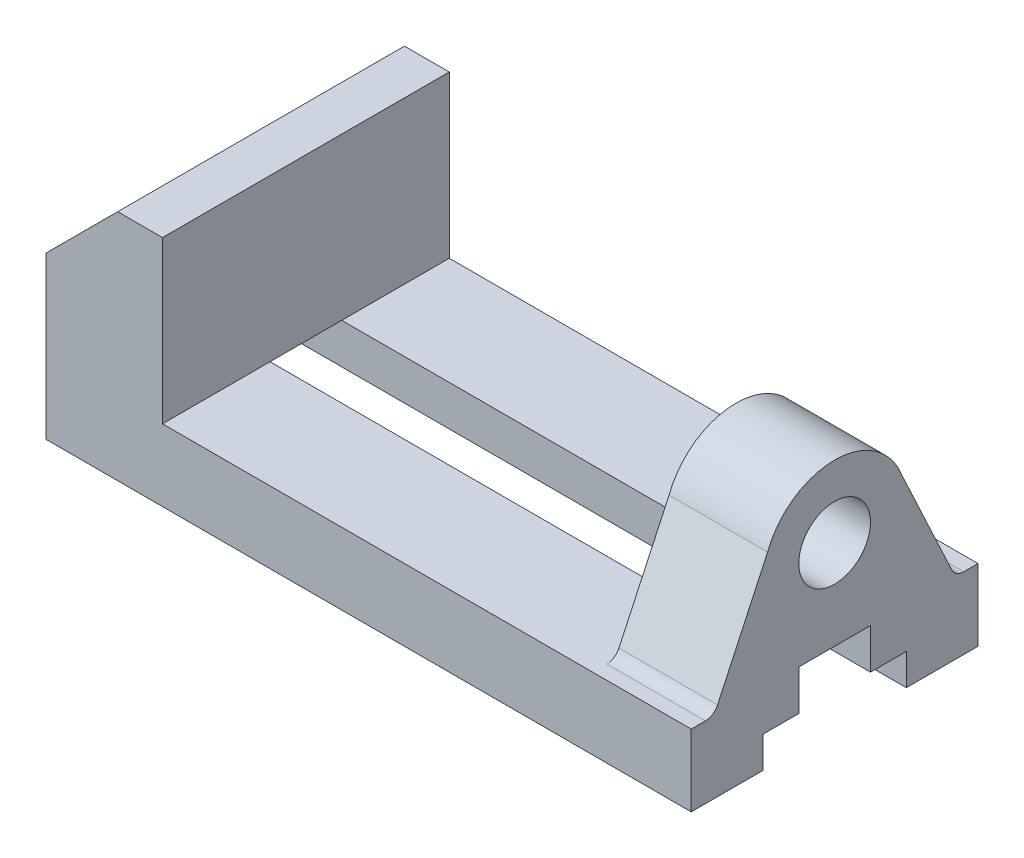
SolidWorks part; units mm, degrees
ref_plane "Front Plane" through (0, 0, 0) normal (0, 0, 1) x (1, 0, 0)
ref_plane "Top Plane" through (0, 0, 0) normal (0, 1, 0) x (1, 0, 0)
ref_plane "Right Plane" through (0, 0, 0) normal (1, 0, 0) x (0, 0, -1)
sketch "Sketch1" plane through (0, 0, 0) normal (0, 1, 0) x (1, 0, 0)
  line L1 (-72, 32) -> (72, 32)
  line L2 (-72, 32) -> (-72, -32)
  line L3 (-72, -32) -> (72, -32)
  line L4 (72, 32) -> (72, -32)
  line L5 (-72, 32) -> (72, -32) construction
  line L6 (-72, -32) -> (72, 32) construction
  point P0 (0, 0)
  dimension "D1" = 64
  dimension "D2" = 144
extrude "Boss-Extrude1" add sketch "Sketch1" along normal blind 16
sketch "Sketch2" plane through (0, 16, 0) normal (0, 1, 0) x (1, 0, 0)
  line L1 (-72, 32) -> (-46, 32)
  line L2 (-72, 32) -> (-72, -32)
  line L3 (-72, -32) -> (-46, -32)
  line L4 (-46, 32) -> (-46, -32)
  dimension "D1" = 26
extrude "Boss-Extrude2" add sketch "Sketch2" along normal blind 36
sketch "Sketch3" plane through (0, 0, 32) normal (0, 0, 1) x (1, 0, 0)
  line L0 (-46, 52) -> (-56, 52)
  line L1 (-72, 52) -> (-46, 52) construction
  line L2 (-56, 52) -> (-72, 36)
  line L3 (-72, 52) -> (-72, 0) construction
  dimension "D1" = 10
  dimension "D3" = 16
extrude "Cut-Extrude1" cut sketch "Sketch3" against normal through all and the other way through all
sketch "Sketch4" plane through (0, 16, 0) normal (0, 1, 0) x (1, 0, 0)
  line L0 (-46, -32) -> (72, -32) construction
  line L1 (72, 32) -> (50, 32)
  line L2 (72, 32) -> (72, -32)
  line L3 (72, -32) -> (50, -32)
  line L4 (50, 32) -> (50, -32)
  dimension "D1" = 22
extrude "Boss-Extrude3" add sketch "Sketch4" along normal blind 36
sketch "Sketch5" plane through (72, 0, 0) normal (1, 0, 0) x (0, 0, -1)
  line L0 (-32, 16) -> (32, 16) construction
  line L1 (-32, 52) -> (-32, 0) construction
  line L2 (32, 52) -> (32, 0) construction
  line L3 (-32, 0) -> (32, 0) construction
  line L4 (-16, 0) -> (-16, 7)
  line L5 (-16, 7) -> (-8, 7)
  line L6 (-8, 7) -> (-8, 16)
  line L7 (-8, 16) -> (8, 16)
  line L8 (8, 16) -> (8, 7)
  line L9 (8, 7) -> (16, 7)
  line L10 (16, 7) -> (16, 0)
  point P10 (0, 0)
  point P17 (0, 0)
  point P19 (0, 16)
  line M1 (-32, 0) -> (32, 0)
  dimension "D1" = 16
  dimension "D2" = 32
  dimension "D3" = 7
  dimension "D4" = 7
  dimension "D5" = 16
  dimension "D6" = 8
extrude "Cut-Extrude2" cut sketch "Sketch5" against normal through all and the other way through all contours L10 L9 L8 L7 L6 L5 L4 M1
sketch "Sketch6" plane through (72, 0, 0) normal (1, 0, 0) x (0, 0, -1)
  line L0 (-32, 16) -> (32, 16) construction
  line L1 (-32, 52) -> (32, 52) construction
  line L2 (-32, 16) -> (-28.8437, 16)
  line L3 (-26.1248, 17.7321) -> (-14.9584, 41.6784)
  line L4 (0, 52) -> (0, 17.0603) construction
  line L5 (26.1248, 17.7321) -> (14.9584, 41.6784)
  line L6 (28.8437, 16) -> (32, 16)
  arc A0 (14.9584, 41.6784) -> (-14.9584, 41.6784) centre (0, 36) ccw
  circle A1 centre (0, 36) radius 8
  arc A2 (26.1248, 17.7321) -> (28.8437, 16) centre (28.8437, 19) ccw
  arc A3 (-28.8437, 16) -> (-26.1248, 17.7321) centre (-28.8437, 19) ccw
  point P17 (26.9325, 16)
  point P20 (-26.9325, 16)
  line M3 (32, 0) -> (32, 52)
  line M4 (32, 52) -> (-32, 52)
  line M5 (-32, 52) -> (-32, 0)
  dimension "D1" = 32
  dimension "D3" = 16
  dimension "D4" = 3
  dimension "D2" = 50
extrude "Cut-Extrude3" cut sketch "Sketch6" against normal blind 36 contours L2 A3 L3 A0 M4 M5 | A1 | L5 A2 L6 A0 M3 M4
hole_wizard "Ø12.0mm Dowel Hole1" positions "Sketch7" profile "Sketch8" hole size "Ø12.0" standard "AS"
sketch "Sketch7" plane through (0, 0, 0) normal (0, -1, 0) x (-1, 0, 0)
  line L0 (72, -16) -> (72, -32) construction
  line L1 (72, 32) -> (72, 16) construction
  point P0 (34, -23.5518)
  point P2 (-36, -23.5518)
  point P4 (-36, 24.9579)
  point P6 (34, 24.9579)
  dimension "D1" = 38
  dimension "D2" = 70
  dimension "D3" = 38
  dimension "D4" = 70
sketch "Sketch8" plane through (-34, 0, 23.5518) normal (1, 0, 0) x (0, 0, -1)
  line L0 (0, 0) -> (0, 13.6052)
  line L1 (0, 13.6052) -> (6, 10)
  line L2 (6, 10) -> (6, 0)
  line L5 (6, 0) -> (0, 0)
  line L10 (0, 13.6052) -> (-6, 10) construction
  line L11 (0, -6.35) -> (0, 107.95) construction
  dimension "Hole Dia." = 12
  dimension "Hole Depth" = 10
  dimension "Drill Angle" = 118
